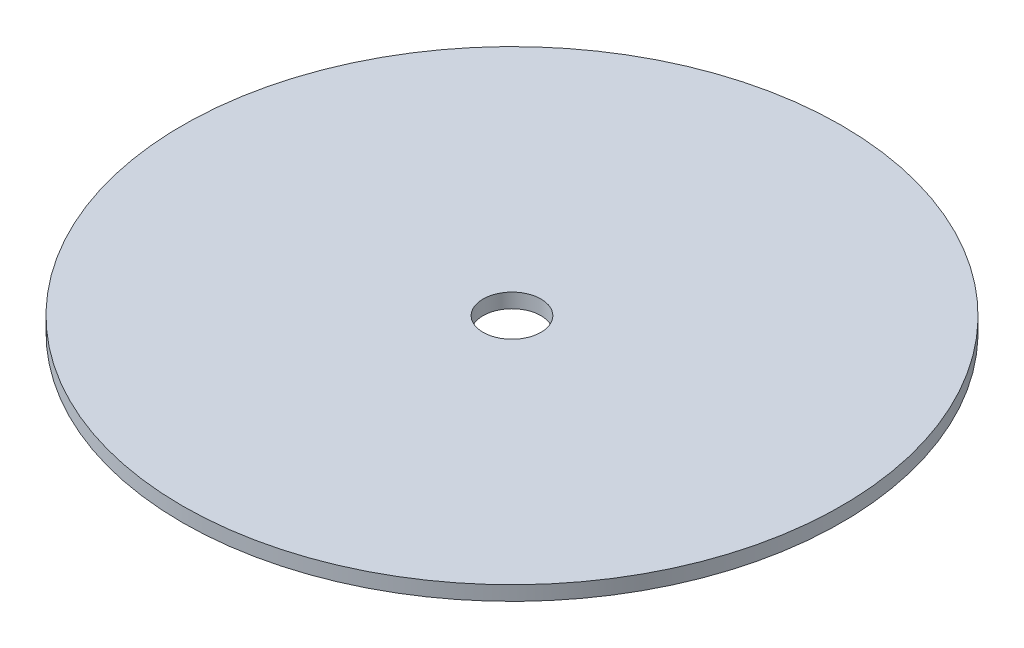
SolidWorks part; units mm, degrees
ref_plane "Front Plane" through (0, 0, 0) normal (0, 0, 1) x (1, 0, 0)
ref_plane "Top Plane" through (0, 0, 0) normal (0, 1, 0) x (1, 0, 0)
ref_plane "Right Plane" through (0, 0, 0) normal (1, 0, 0) x (0, 0, -1)
sketch "Sketch1" plane through (0, 0, 0) normal (0, 1, 0) x (1, 0, 0)
  circle A0 centre (0, 0) radius 72.39
  dimension "D1" = 144.78
extrude "Boss-Extrude1" add sketch "Sketch1" along normal blind 3.175
sketch "Sketch2" plane through (0, 3.175, 0) normal (0, 1, 0) x (1, 0, 0)
  circle A0 centre (0, 0) radius 6.35
  dimension "D1" = 12.7
extrude "Cut-Extrude1" cut sketch "Sketch2" against normal through all
